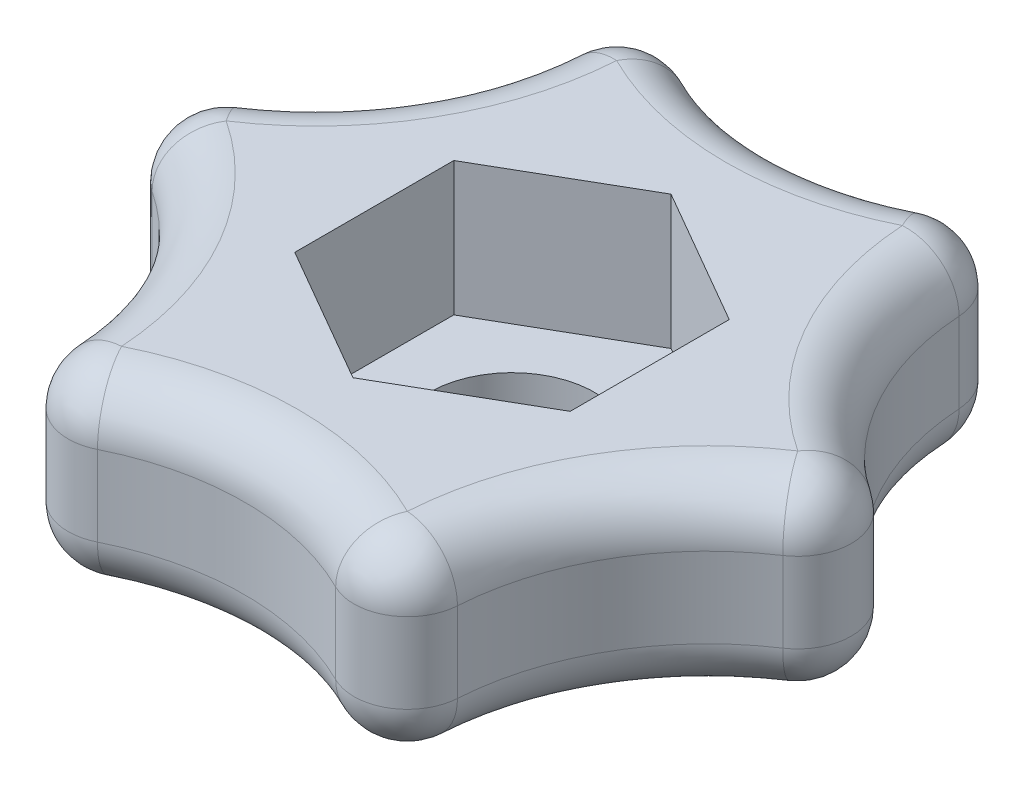
SolidWorks part; units mm, degrees
ref_plane "Front Plane" through (0, 0, 0) normal (0, 0, 1) x (1, 0, 0)
ref_plane "Top Plane" through (0, 0, 0) normal (0, 1, 0) x (1, 0, 0)
ref_plane "Right Plane" through (0, 0, 0) normal (1, 0, 0) x (0, 0, -1)
sketch "Sketch1" plane through (0, 0, 0) normal (0, 1, 0) x (1, 0, 0)
  arc A2 (-8.6603, 15) -> (8.6603, 15) centre (0, 20) ccw
  arc A3 (-17.3205, 0) -> (-8.6603, 15) centre (-17.3205, 10) ccw
  arc A4 (-8.6603, -15) -> (-17.3205, 0) centre (-17.3205, -10) ccw
  arc A5 (8.6603, 15) -> (17.3205, 0) centre (17.3205, 10) ccw
  arc A6 (17.3205, 0) -> (8.6603, -15) centre (17.3205, -10) ccw
  arc A7 (8.6603, -15) -> (-8.6603, -15) centre (0, -20) ccw
  point P11 (0, 0)
extrude "Boss-Extrude1" add sketch "Sketch1" along normal blind 7
sketch "Sketch2" plane through (0, 7, 0) normal (0, 1, 0) x (1, 0, 0)
  line L1 (0, -5.9467) -> (5.15, -2.9734)
  line L2 (5.15, -2.9734) -> (5.15, 2.9734)
  line L3 (5.15, 2.9734) -> (0, 5.9467)
  line L4 (0, 5.9467) -> (-5.15, 2.9734)
  line L5 (-5.15, 2.9734) -> (-5.15, -2.9734)
  line L6 (-5.15, -2.9734) -> (0, -5.9467)
  circle A0 centre (0, 0) radius 5.15 construction
  dimension "D1" = 10.3
extrude "Cut-Extrude1" cut sketch "Sketch2" against normal blind 5 from surface at 0 contours L5 L6 L1 L2 L3 L4 starting at face at (0, 7, 0)
sketch "Sketch3" plane through (0, 2, 0) normal (0, 1, 0) x (1, 0, 0)
  circle A0 centre (0, 0) radius 3.1
extrude "Cut-Extrude2" cut sketch "Sketch3" against normal through all
fillet "Fillet1" radius 2 18 edges at (-17.3205, 3.5, 0) (-8.6603, 3.5, 15) (8.6603, 3.5, 15) (17.3205, 3.5, 0) (8.6603, 3.5, -15) (-8.6603, 3.5, -15) (8.6603, 0, -5) (8.6603, 0, 5) (0, 0, 10) (-8.6603, 0, -5) (-8.6603, 0, 5) (0, 0, -10) (-8.6603, 7, 5) (0, 7, 10) (8.6603, 7, 5) (8.6603, 7, -5) (0, 7, -10) (-8.6603, 7, -5)
